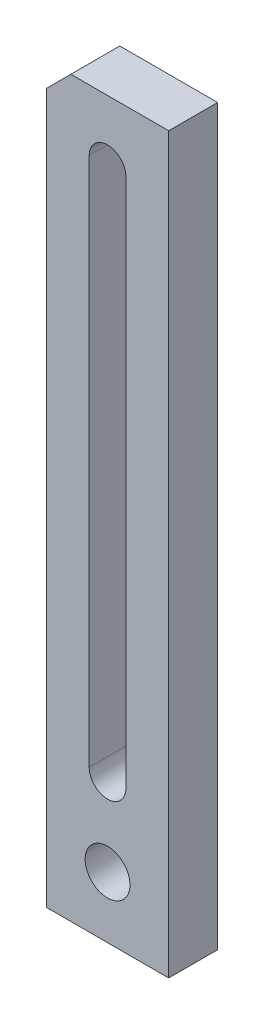
SolidWorks part; units mm, degrees
ref_plane "前视基准面" through (0, 0, 0) normal (0, 0, 1) x (1, 0, 0)
ref_plane "上视基准面" through (0, 0, 0) normal (0, 1, 0) x (1, 0, 0)
ref_plane "右视基准面" through (0, 0, 0) normal (1, 0, 0) x (0, 0, -1)
sketch "草图1" plane through (0, 0, 0) normal (0, 0, 1) x (1, 0, 0)
  line L1 (-15, 90) -> (15, 90)
  line L2 (-15, 90) -> (-15, -90)
  line L3 (-15, -90) -> (15, -90)
  line L4 (15, 90) -> (15, -90)
  line L5 (-15, 90) -> (15, -90) construction
  line L6 (-15, -90) -> (15, 90) construction
  point P0 (0, 0)
  dimension "D1" = 30
  dimension "D2" = 180
extrude "凸台-拉伸1" add sketch "草图1" along normal blind 12
sketch "草图2" plane through (0, 0, 12) normal (0, 0, 1) x (1, 0, 0)
  line L0 (0, 75) -> (0, -55) construction
  line L1 (4.5, 75) -> (4.5, -55)
  line L2 (-4.5, 75) -> (-4.5, -55)
  line L3 (-15, -90) -> (15, -90) construction
  line L4 (-15, 90) -> (-15, -90) construction
  arc A0 (4.5, 75) -> (-4.5, 75) centre (0, 75) ccw
  arc A1 (-4.5, -55) -> (4.5, -55) centre (0, -55) ccw
  circle A2 centre (0, -75) radius 5.5
  point P3 (0, 10)
  dimension "D4" = 11
  dimension "D1" = 9
  dimension "D2" = 130
  dimension "D3" = 20
  dimension "D5" = 15
  dimension "D6" = 15
extrude "切除-拉伸1" cut sketch "草图2" against normal blind 12
chamfer "倒角1" distance 6 angle 45 1 edges at (-15, 90, 6)
